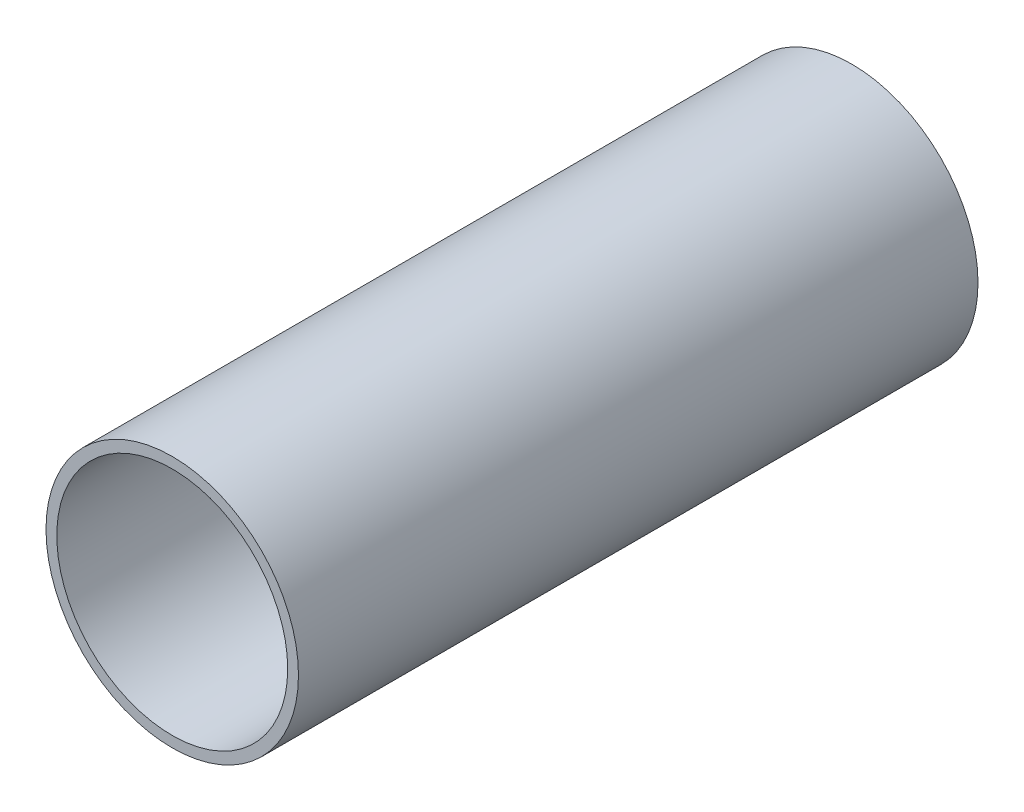
SolidWorks part; units mm, degrees
material "PVC Rigid"
ref_plane "Front Plane" through (0, 0, 0) normal (0, 0, 1) x (1, 0, 0)
ref_plane "Top Plane" through (0, 0, 0) normal (0, 1, 0) x (1, 0, 0)
ref_plane "Right Plane" through (0, 0, 0) normal (1, 0, 0) x (0, 0, -1)
sketch "Sketch1" plane through (0, 0, 0) normal (0, 0, 1) x (1, 0, 0)
  circle A1 centre (0, 0) radius 84.9312
  circle A2 centre (0, 0) radius 77.6812
  dimension "D1" = 7.25
extrude "Boss-Extrude1" add sketch "Sketch1" along normal blind 457.2
ref_plane "Plane1" through (0, 0, 228.6) normal (0, 0, 1) x (1, 0, 0)
